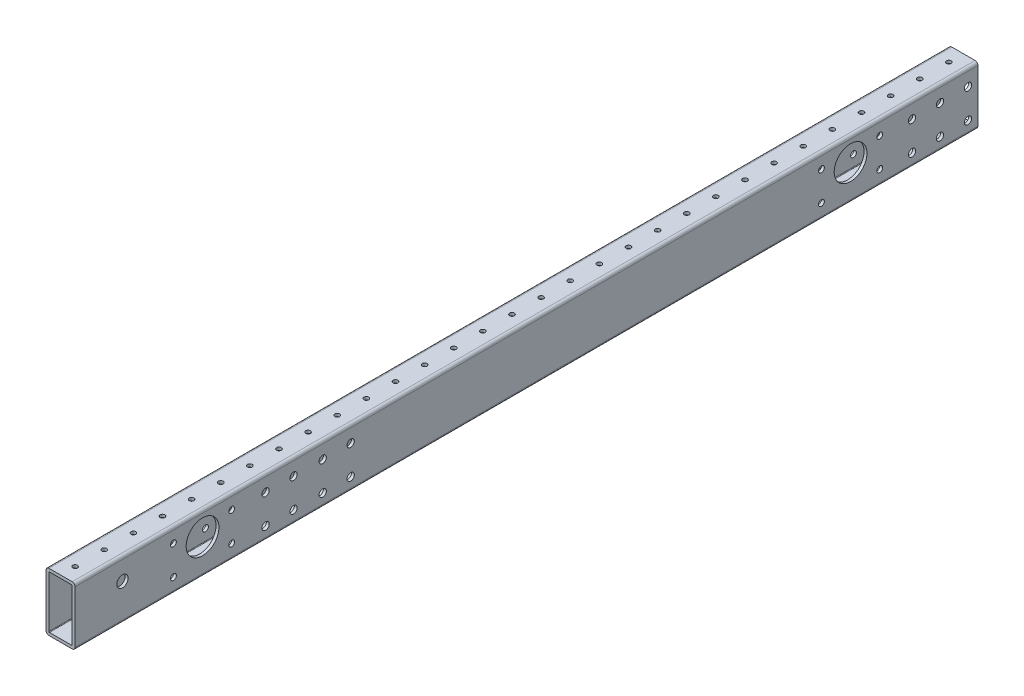
SolidWorks part; units mm, degrees
material "1060 Alloy"
ref_plane "Front Plane" through (0, 0, 0) normal (0, 0, 1) x (1, 0, 0)
ref_plane "Top Plane" through (0, 0, 0) normal (0, 1, 0) x (1, 0, 0)
ref_plane "Right Plane" through (0, 0, 0) normal (1, 0, 0) x (0, 0, -1)
ref_plane "Plane1" through (12.7, 0, 0) normal (1, 0, 0) x (0, 0, -1)
sketch "Sketch1" plane through (12.7, 0, 0) normal (1, 0, 0) x (0, 0, -1)
  line L0 (393.7, -25.4) -> (393.7, 25.4)
  line L1 (393.7, 25.4) -> (-393.7, 25.4)
  line L2 (-393.7, 25.4) -> (-393.7, -25.4)
  line L3 (-393.7, -25.4) -> (393.7, -25.4)
  point P5 (0, 25.4)
  dimension "D1" = 50.8
  dimension "D2" = 25.4
  dimension "D3" = 787.4
extrude "Boss-Extrude1" add sketch "Sketch1" against normal blind 25.4
sketch "Sketch2" plane through (0, 0, -393.7) normal (0, 0, -1) x (-1, 0, 0)
  line L0 (10.16, -22.86) -> (10.16, 22.86)
  line L1 (10.16, 22.86) -> (-10.16, 22.86)
  line L2 (-10.16, 22.86) -> (-10.16, -22.86)
  line L3 (-10.16, -22.86) -> (10.16, -22.86)
extrude "Cut-Extrude1" cut sketch "Sketch2" against normal through all
hole_wizard "#6 Clearance Hole1" positions "Sketch4" profile "Sketch3" hole size "#6" standard "ANSI Inch"
sketch "Sketch4" plane through (0, -25.4, 0) normal (0, -1, 0) x (-1, 0, 0)
  point P0 (0, 711.2)
  point P1 (0, 736.6)
  point P2 (0, 685.8)
  point P3 (0, 660.4)
  point P4 (0, 635)
  point P5 (0, 609.6)
  point P6 (0, 584.2)
  point P7 (0, 558.8)
  point P8 (0, 533.4)
  point P9 (0, 508)
  point P10 (0, 482.6)
  point P11 (0, 457.2)
  point P12 (0, 431.8)
  point P13 (0, 406.4)
  point P14 (0, 381)
  point P15 (0, 355.6)
  point P16 (0, 330.2)
  point P17 (0, 304.8)
  point P18 (0, 279.4)
  point P19 (0, 254)
  point P20 (0, 228.6)
  point P21 (0, 203.2)
  point P22 (0, 177.8)
  point P23 (0, 152.4)
  point P24 (0, 127)
  point P25 (0, 101.6)
  point P26 (0, 76.2)
  point P27 (0, 50.8)
  point P28 (0, 25.4)
  point P29 (0, 0)
  point P30 (0, -25.4)
  point P31 (0, -50.8)
  point P32 (0, -76.2)
  point P33 (0, -101.6)
  point P34 (0, -127)
  point P35 (0, -152.4)
  point P36 (0, -177.8)
  point P37 (0, -203.2)
  point P38 (0, -228.6)
  point P39 (0, -254)
  point P40 (0, -279.4)
  point P41 (0, -304.8)
  point P42 (0, -330.2)
  point P43 (0, -355.6)
  point P44 (0, -381)
  point P45 (0, -406.4)
  point P46 (0, -431.8)
  point P47 (0, -457.2)
  point P48 (0, -482.6)
  point P49 (0, -508)
  point P50 (0, -533.4)
  point P51 (0, -558.8)
  point P52 (0, -584.2)
  point P53 (0, -609.6)
  point P54 (0, -635)
  point P55 (0, -660.4)
  point P56 (0, -685.8)
  point P57 (0, -711.2)
  point P58 (0, -736.6)
sketch "Sketch3" plane through (0, -25.4, -711.2) normal (1, 0, 0) x (0, 0, -1)
  line L0 (0, 0) -> (0, 50.8)
  line L1 (0, 50.8) -> (2.0701, 50.8)
  line L2 (2.0701, 50.8) -> (2.0701, 0)
  line L5 (2.0701, 0) -> (0, 0)
  line L11 (0, -6.35) -> (0, 107.95) construction
  dimension "Thru Hole Dia." = 4.1402
  dimension "Thru Hole Depth" = 50.8
hole_wizard "#6 Clearance Hole2" positions "Sketch6" profile "Sketch5" hole size "#6" standard "ANSI Inch"
sketch "Sketch6" plane through (0, 25.4, 0) normal (0, 1, 0) x (1, 0, 0)
  point P0 (0, 711.2)
  point P1 (0, 736.6)
  point P2 (0, 685.8)
  point P3 (0, 660.4)
  point P4 (0, 635)
  point P5 (0, 609.6)
  point P6 (0, 584.2)
  point P7 (0, 558.8)
  point P8 (0, 533.4)
  point P9 (0, 508)
  point P10 (0, 482.6)
  point P11 (0, 457.2)
  point P12 (0, 431.8)
  point P13 (0, 406.4)
  point P14 (0, 381)
  point P15 (0, 355.6)
  point P16 (0, 330.2)
  point P17 (0, 304.8)
  point P18 (0, 279.4)
  point P19 (0, 254)
  point P20 (0, 228.6)
  point P21 (0, 203.2)
  point P22 (0, 177.8)
  point P23 (0, 152.4)
  point P24 (0, 127)
  point P25 (0, 101.6)
  point P26 (0, 76.2)
  point P27 (0, 50.8)
  point P28 (0, 25.4)
  point P29 (0, 0)
  point P30 (0, -25.4)
  point P31 (0, -50.8)
  point P32 (0, -76.2)
  point P33 (0, -101.6)
  point P34 (0, -127)
  point P35 (0, -152.4)
  point P36 (0, -177.8)
  point P37 (0, -203.2)
  point P38 (0, -228.6)
  point P39 (0, -254)
  point P40 (0, -279.4)
  point P41 (0, -304.8)
  point P42 (0, -330.2)
  point P43 (0, -355.6)
  point P44 (0, -381)
  point P45 (0, -406.4)
  point P46 (0, -431.8)
  point P47 (0, -457.2)
  point P48 (0, -482.6)
  point P49 (0, -508)
  point P50 (0, -533.4)
  point P51 (0, -558.8)
  point P52 (0, -584.2)
  point P53 (0, -609.6)
  point P54 (0, -635)
  point P55 (0, -660.4)
  point P56 (0, -685.8)
  point P57 (0, -711.2)
  point P58 (0, -736.6)
sketch "Sketch5" plane through (0, 25.4, -711.2) normal (1, 0, 0) x (0, 0, 1)
  line L0 (0, 0) -> (0, 50.8)
  line L1 (0, 50.8) -> (2.0701, 50.8)
  line L2 (2.0701, 50.8) -> (2.0701, 0)
  line L5 (2.0701, 0) -> (0, 0)
  line L11 (0, -6.35) -> (0, 107.95) construction
  dimension "Thru Hole Dia." = 4.1402
  dimension "Thru Hole Depth" = 50.8
fillet "Fillet1" radius 0.5 4 edges at (10.16, 22.86, 0) (-10.16, -22.86, 0) (-10.16, 22.86, 0) (10.16, -22.86, 0)
fillet "Fillet2" radius 2.54 4 edges at (12.7, 25.4, 0) (-12.7, -25.4, 0) (12.7, -25.4, 0) (-12.7, 25.4, 0)
sketch "Sketch7" plane through (12.7, 0, 0) normal (1, 0, 0) x (0, 0, -1)
  line L0 (0, 0) -> (0, 22.86) construction
  line L1 (-393.7, 22.86) -> (393.7, 22.86) construction
  line L3 (-393.7, -25.4) -> (393.7, -25.4) construction
  circle A0 centre (282.575, 5.08) radius 14.3002
  circle A1 centre (-282.575, 5.08) radius 14.3002
  dimension "D1" = 28.6004
  dimension "D2" = 30.48
  dimension "D3" = 282.575
extrude "Cut-Extrude2" cut sketch "Sketch7" against normal through all both and the other way through all
sketch "Sketch8" plane through (0, 0, 0) normal (1, 0, 0) x (0, 0, -1)
  line L3 (393.7, -25.4) -> (-393.7, -25.4) construction
  line L4 (-393.7, 22.86) -> (-393.7, -22.86) construction
  line L5 (393.7, -22.86) -> (393.7, 22.86) construction
  circle A1 centre (-153.3881, 11.1125) radius 3.1877
  circle A2 centre (-153.3881, -14.2875) radius 3.1877
  circle A3 centre (-227.6094, 11.1125) radius 3.1877
  circle A4 centre (-227.6094, -14.2875) radius 3.1877
  circle A5 centre (336.1411, 11.1125) radius 3.1877
  circle A6 centre (336.1411, -14.2875) radius 3.1877
  circle A7 centre (384.9624, 11.1125) radius 3.1877
  circle A8 centre (384.9624, -14.2875) radius 3.1877
  circle A9 centre (-203.2, 11.1125) radius 3.1877
  circle A10 centre (-203.2, -14.2875) radius 3.1877
  circle A11 centre (-177.8, 11.1125) radius 3.1877
  circle A12 centre (-177.8, -14.2875) radius 3.1877
  circle A13 centre (360.553, 11.1125) radius 3.1877
  circle A14 centre (360.553, -14.2875) radius 3.1877
  dimension "D1" = 6.3754
  dimension "D2" = 240.3119
  dimension "D3" = 36.5125
  dimension "D4" = 25.4
  dimension "D5" = 74.2213
  dimension "D6" = 57.5589
  dimension "D7" = 48.8213
  dimension "D8" = 190.5
  dimension "D9" = 25.4
  dimension "D10" = 33.147
extrude "Cut-Extrude3" cut sketch "Sketch8" against normal through all both and the other way through all
sketch "Sketch9" plane through (0, 0, 0) normal (1, 0, 0) x (0, 0, -1)
  line L0 (393.7, -22.86) -> (393.7, 22.86) construction
  circle A0 centre (88.9, 0) radius 14.2875
  dimension "D1" = 28.575
  dimension "D2" = 304.8
extrude "Cut-Extrude4" [suppressed] cut sketch "Sketch9" against normal through all both and the other way through all
sketch "Sketch11" plane through (-12.7, 0, 0) normal (-1, 0, 0) x (0, 0, 1)
  arc A0 (-305.4223, 12.7) -> (-310.5277, 12.7) centre (-307.975, 12.7) ccw construction
  arc A1 (-310.5277, 12.7) -> (-305.4223, 12.7) centre (-307.975, 12.7) ccw construction
  arc A2 (-305.4223, 12.7) -> (-310.5277, 12.7) centre (-307.975, 12.7) ccw
  arc A3 (-310.5277, 12.7) -> (-305.4223, 12.7) centre (-307.975, 12.7) ccw
  arc A4 (-310.5277, -12.7) -> (-305.4223, -12.7) centre (-307.975, -12.7) ccw construction
  arc A5 (-305.4223, -12.7) -> (-310.5277, -12.7) centre (-307.975, -12.7) ccw construction
  arc A6 (-310.5277, -12.7) -> (-305.4223, -12.7) centre (-307.975, -12.7) ccw
  arc A7 (-305.4223, -12.7) -> (-310.5277, -12.7) centre (-307.975, -12.7) ccw
  arc A8 (-259.7277, -12.7) -> (-254.6223, -12.7) centre (-257.175, -12.7) ccw construction
  arc A9 (-254.6223, -12.7) -> (-259.7277, -12.7) centre (-257.175, -12.7) ccw construction
  arc A10 (-259.7277, 12.7) -> (-254.6223, 12.7) centre (-257.175, 12.7) ccw construction
  arc A11 (-254.6223, 12.7) -> (-259.7277, 12.7) centre (-257.175, 12.7) ccw construction
  arc A12 (-259.7277, -12.7) -> (-254.6223, -12.7) centre (-257.175, -12.7) ccw
  arc A13 (-254.6223, -12.7) -> (-259.7277, -12.7) centre (-257.175, -12.7) ccw
  arc A14 (-259.7277, 12.7) -> (-254.6223, 12.7) centre (-257.175, 12.7) ccw
  arc A15 (-254.6223, 12.7) -> (-259.7277, 12.7) centre (-257.175, 12.7) ccw
sketch "Sketch10" plane through (0, 0, 0) normal (1, 0, 0) x (0, 0, -1)
  line L0 (0, -25.4) -> (0, 25.4) construction
  line L1 (307.975, 12.7) -> (307.975, -12.7) construction
  line L2 (307.975, 12.7) -> (257.175, 12.7) construction
  line L4 (-393.7, -25.4) -> (393.7, -25.4) construction
  line L6 (393.7, 25.4) -> (-393.7, 25.4) construction
  circle A0 centre (307.975, 12.7) radius 2.5527
  circle A1 centre (307.975, -12.7) radius 2.5527
  circle A2 centre (257.175, 12.7) radius 2.5527
  circle A3 centre (257.175, -12.7) radius 2.5527
  circle A4 centre (-257.175, -12.7) radius 2.5527
  circle A10 centre (-307.975, -12.7) radius 2.5527
  circle A11 centre (-257.175, -12.7) radius 2.5527
  circle A12 centre (-257.175, 12.7) radius 2.5527
  circle A13 centre (-307.975, 12.7) radius 2.5527
  point P24 (282.575, 5.08)
  point P26 (282.575, 12.7)
  dimension "D1" = 5.1054
  dimension "D2" = 50.8
  dimension "D3" = 25.4
  dimension "D4" = 7.62
extrude "Cut-Extrude5" cut sketch "Sketch10" against normal through all both and the other way through all contours A0 | A2 | A1 | A3 | A12 | A4 | A13 | A10
sketch "Sketch12" plane through (-12.7, 0, 0) normal (-1, 0, 0) x (0, 0, 1)
  line L1 (393.7, -25.4) -> (-393.7, -25.4) construction
  circle A1 centre (352.425, 6.35) radius 4.953
  circle A3 centre (282.575, 5.08) radius 14.3002 construction
  point P4 (319.3015, 15.2178)
  dimension "D1" = 9.906
  dimension "D2" = 69.85
  dimension "D3" = 31.75
  dimension "D4" = 38.1
  dimension "D5" = 34.29
extrude "Cut-Extrude6" cut sketch "Sketch12" against normal through all
